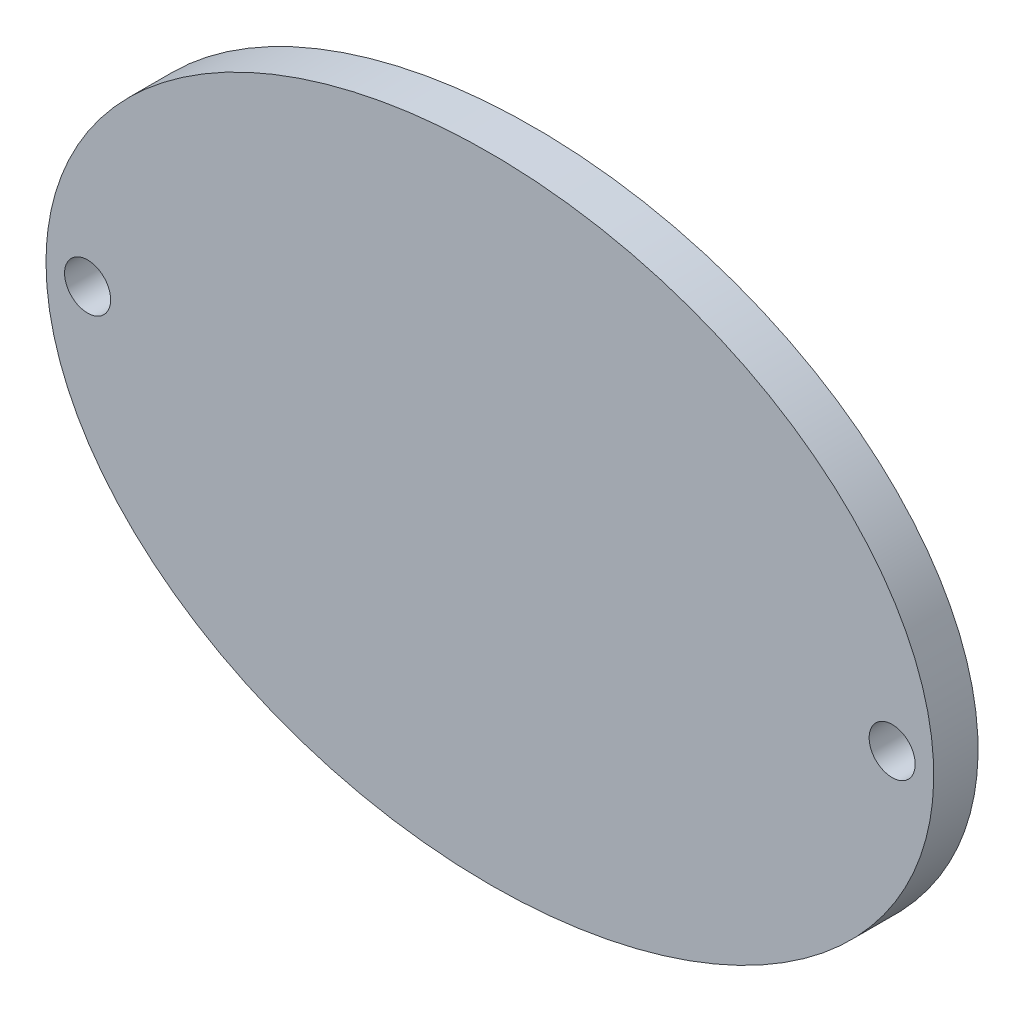
SolidWorks part; units mm, degrees
material "Acrylic (Medium-high impact)"
ref_plane "Plan de face" through (0, 0, 0) normal (0, 0, 1) x (1, 0, 0)
ref_plane "Plan de dessus" through (0, 0, 0) normal (0, 1, 0) x (1, 0, 0)
ref_plane "Plan de droite" through (0, 0, 0) normal (1, 0, 0) x (0, 0, -1)
sketch "Sketch1" plane through (0, 0, 0) normal (0, 0, 1) x (1, 0, 0)
  ellipse E0 centre (0, 0) end of major axis (-31.8, 0) minor radius 22.7
  dimension "D1" = 45.4
  dimension "D2" = 63.6
extrude "Boss-Extrude1" add sketch "Sketch1" along normal blind 3.175
sketch "Sketch2" plane through (0, 0, 0) normal (0, 0, -1) x (-1, 0, 0)
  line L0 (-28.82, 0) -> (28.82, 0) construction
  circle A0 centre (-28.82, 0) radius 1.65
  circle A1 centre (28.82, 0) radius 1.65
  point P4 (0, 0)
  dimension "D2" = 3.3
  dimension "D3" = 3.3
  dimension "D1" = 57.64
extrude "Cut-Extrude1" cut sketch "Sketch2" against normal blind 3.175
